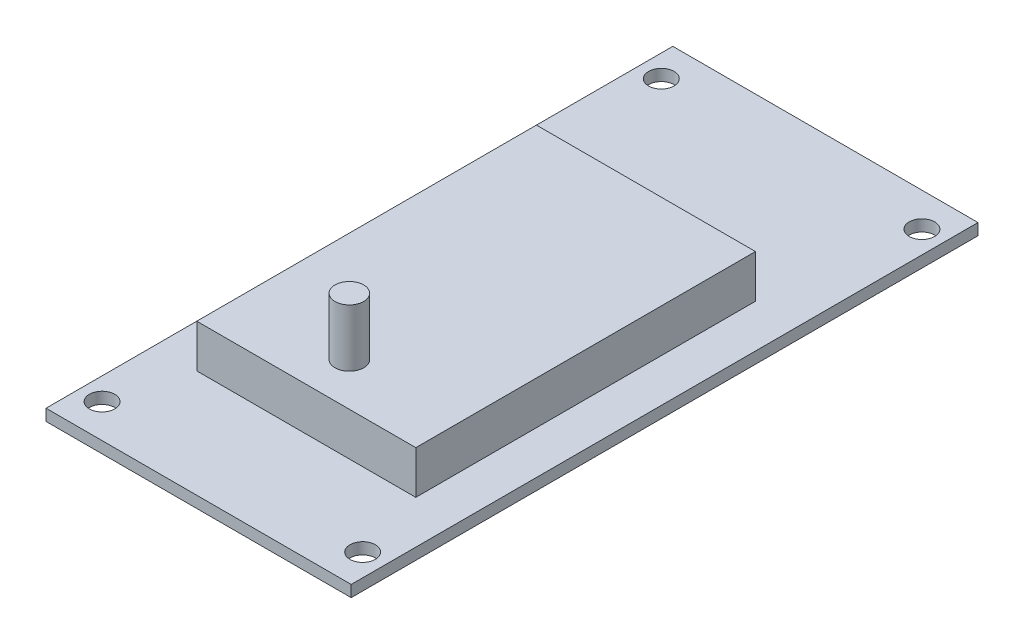
SolidWorks part; units mm, degrees
ref_plane "Front Plane" through (0, 0, 0) normal (0, 0, 1) x (1, 0, 0)
ref_plane "Top Plane" through (0, 0, 0) normal (0, 1, 0) x (1, 0, 0)
ref_plane "Right Plane" through (0, 0, 0) normal (1, 0, 0) x (0, 0, -1)
sketch "Sketch1" plane through (0, 0, 0) normal (0, 1, 0) x (1, 0, 0)
  line L0 (3.105, 82.605) -> (0, 87.31) construction
  line L1 (0, 0) -> (42.51, 0)
  line L2 (0, 0) -> (0, 87.31)
  line L3 (0, 87.31) -> (42.51, 87.31)
  line L4 (42.51, 0) -> (42.51, 87.31)
  line L5 (3.105, 82.605) -> (39.405, 82.605) construction
  line L6 (3.105, 82.605) -> (3.105, 4.705) construction
  line L7 (3.105, 4.705) -> (39.405, 4.705) construction
  line L8 (39.405, 82.605) -> (39.405, 4.705) construction
  line L9 (39.405, 82.605) -> (42.51, 87.31) construction
  line L10 (39.405, 4.705) -> (42.51, 0) construction
  line L11 (3.105, 4.705) -> (0, 0) construction
  circle A0 centre (3.105, 82.605) radius 1.77
  circle A1 centre (39.405, 82.605) radius 1.77
  circle A2 centre (3.105, 4.705) radius 1.77
  circle A3 centre (39.405, 4.705) radius 1.77
  dimension "D2" = 3.54
  dimension "D1" = 87.31
  dimension "42.51" = 42.51
  dimension "D3" = 77.9
  dimension "D4" = 36.3
extrude "Boss-Extrude1" add sketch "Sketch1" along normal blind 1.6
sketch "Sketch2" plane through (0, 1.6, 0) normal (0, 1, 0) x (1, 0, 0)
  line L0 (0, 87.31) -> (0, 0) construction
  line L1 (6, 62.31) -> (36.51, 62.31)
  line L2 (6, 62.31) -> (6, 15)
  line L3 (6, 15) -> (36.51, 15)
  line L4 (36.51, 62.31) -> (36.51, 15)
  line L5 (42.51, 0) -> (42.51, 87.31) construction
  line L6 (0, 0) -> (42.51, 0) construction
  line L7 (42.51, 87.31) -> (0, 87.31) construction
  dimension "D1" = 6
  dimension "D2" = 6
  dimension "D3" = 15
  dimension "D4" = 25
extrude "Boss-Extrude2" add sketch "Sketch2" along normal blind 6
sketch "Sketch4" plane through (0, 7.6, 0) normal (0, 1, 0) x (1, 0, 0)
  line L0 (6, 21) -> (36.51, 21) construction
  line L1 (6, 62.31) -> (6, 15) construction
  line L2 (36.51, 15) -> (36.51, 62.31) construction
  line L3 (0, 0) -> (42.51, 0) construction
  circle A0 centre (21.255, 21) radius 2
  dimension "D1" = 4
  dimension "D2" = 21
extrude "Boss-Extrude3" add sketch "Sketch4" along normal blind 8
